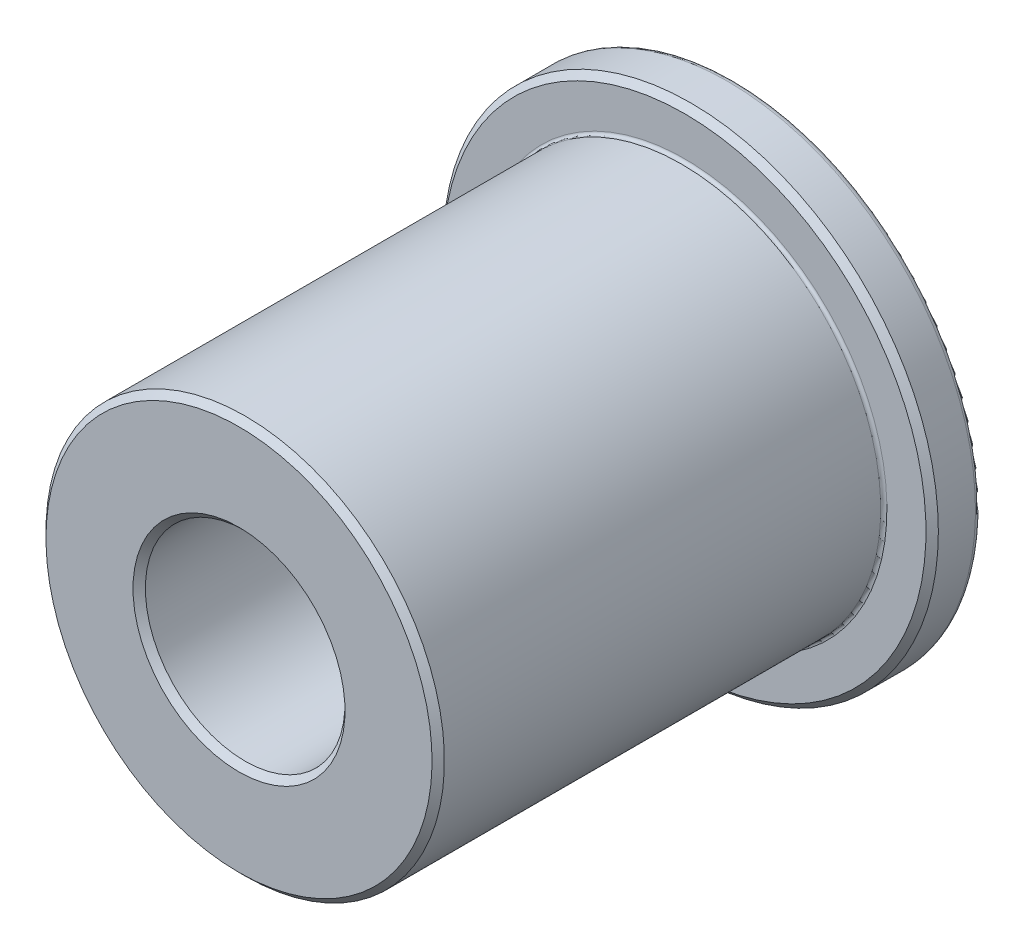
SolidWorks part; units mm, degrees
ref_plane "Front Plane" through (0, 0, 0) normal (0, 0, 1) x (1, 0, 0)
ref_plane "Top Plane" through (0, 0, 0) normal (0, 1, 0) x (1, 0, 0)
ref_plane "Right Plane" through (0, 0, 0) normal (1, 0, 0) x (0, 0, -1)
sketch "Sketch1" plane through (0, 0, 0) normal (0, 0, 1) x (1, 0, 0)
  circle A0 centre (0, 0) radius 3.2004
  circle A1 centre (0, 0) radius 6.3881
  circle A2 centre (0, 0) radius 7.9375
  point P5 (0, 6.3881)
  point P6 (0, 3.2004)
  point P7 (0, 7.9375)
  dimension "ID" = 6.4008
  dimension "OD" = 12.7762
  dimension "Flange OD" = 15.875
sketch "Sketch2" plane through (0, 0, 0) normal (1, 0, 0) x (0, 0, -1)
  line L0 (7.9375, 0) -> (-7.9375, 0)
  line L1 (7.9375, 0) -> (7.9375, 7.9375)
  line L2 (7.9375, 7.9375) -> (6.35, 7.9375)
  line L3 (6.35, 7.9375) -> (6.35, 6.3881)
  line L4 (6.35, 6.3881) -> (-7.9375, 6.3881)
  line L5 (-7.9375, 6.3881) -> (-7.9375, 3.2004)
  line L6 (-7.9375, 3.2004) -> (7.9375, 3.2004)
  point P4 (0, 0)
  dimension "Flange Thickness" = 1.5875
  dimension "Length" = 15.875
sketch "Sketch3" plane through (0, 0, 0) normal (1, 0, 0) x (0, 0, -1)
  line L0 (7.9375, 7.9375) -> (6.35, 7.9375) construction
  line L1 (6.35, 7.9375) -> (6.35, 6.3881) construction
  line L2 (6.35, 6.3881) -> (-7.9375, 6.3881) construction
  line L3 (-7.9375, 3.2004) -> (7.9375, 3.2004) construction
  line L4 (-7.9375, 6.3881) -> (-7.9375, 3.2004) construction
  line L5 (7.9375, 7.9375) -> (6.35, 7.9375)
  line L6 (6.35, 7.9375) -> (6.35, 6.3881)
  line L7 (6.35, 6.3881) -> (-7.9375, 6.3881)
  line L8 (-7.9375, 3.2004) -> (7.9375, 3.2004)
  line L9 (-7.9375, 6.3881) -> (-7.9375, 3.2004)
  line L10 (7.9375, 7.9375) -> (7.9375, 3.2004)
revolve "Revolve1" add sketch "Sketch3" angle 360 about L0
chamfer "Chamfer1" distance 0.1984 angle 45 3 edges at (0, 7.9375, -6.35) (0, 6.3881, 7.9375) (0, 3.2004, 7.9375)
fillet "Fillet1" radius 0.1984 1 edges at (0, 7.9375, -7.9375)
fillet "Fillet2" radius 0.0992 1 edges at (0, 6.3881, -6.35)
equation "\"D1@Chamfer1\"=\"Flange Thickness@Sketch2\"*.125"
equation "\"D1@Fillet1\"=\"D1@Chamfer1\""
equation "\"D1@Fillet2\"=\"D1@Fillet1\"*.5"
